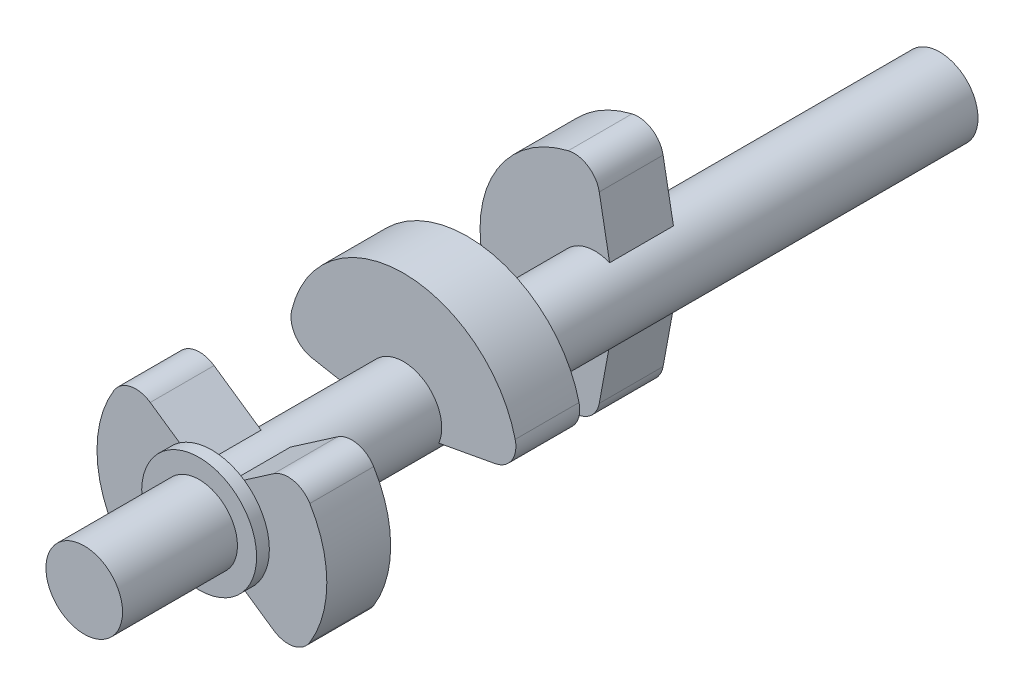
SolidWorks part; units mm, degrees
ref_plane "Спереди" through (0, 0, 0) normal (0, 0, 1) x (1, 0, 0)
ref_plane "Сверху" through (0, 0, 0) normal (0, 1, 0) x (1, 0, 0)
ref_plane "Справа" through (0, 0, 0) normal (1, 0, 0) x (0, 0, -1)
sketch "Эскиз2" plane through (0, 0, 0) normal (0, 0, 1) x (1, 0, 0)
  circle A0 centre (0, 0) radius 1.5
  dimension "D1" = 3
extrude "shaft" add sketch "Эскиз2" along normal blind 33.5
ref_plane "excentric1plane" through (0, 0, 11) normal (0, 0, -1) x (-1, 0, 0)
sketch "Эскиз3" plane through (0, 0, 11) normal (0, 0, -1) x (-1, 0, 0)
  line L0 (1.7221, 4.1575) -> (0, 0) construction
  line L1 (0, 4.5) -> (0, 0) construction
  line L2 (3.182, 3.182) -> (0, 0) construction
  line L3 (4.1575, 1.7221) -> (0, 0) construction
  line L4 (4.5, 0) -> (0, 0) construction
  line L5 (4.1575, -1.7221) -> (0, 0) construction
  line L6 (3.182, -3.182) -> (0, 0) construction
  line L7 (1.7221, -4.1575) -> (0, 0) construction
  line L8 (0, -4.5) -> (0, 0) construction
  line L9 (-1.2555, -3.031) -> (-0.574, -1.3858) construction
  line L10 (-3.182, -3.182) -> (0, 0) construction
  line L11 (-4.1575, -1.7221) -> (0, 0) construction
  line L12 (-4.5, 0) -> (0, 0) construction
  line L13 (-4.1575, 1.7221) -> (0, 0) construction
  line L14 (-3.182, 3.182) -> (0, 0) construction
  line L15 (-1.2555, 3.031) -> (-0.574, 1.3858) construction
  line L16 (0, 4.5) -> (-0.574, 1.3858)
  line L17 (0, -4.5) -> (-0.574, -1.3858)
  circle A0 centre (0, 0) radius 4.5
  circle A1 centre (0, 0) radius 1.5
  point P21 (0, 0)
  dimension "D2" = 9
  dimension "D1" = 16
ref_plane "excentric2plane" through (0, 0, 18.5) normal (0, 0, -1) x (-1, 0, 0)
ref_plane "excentric3plane" through (0, 0, 26) normal (0, 0, -1) x (-1, 0, 0)
sketch "excentric2sketch" plane through (0, 0, 18.5) normal (0, 0, -1) x (-1, 0, 0)
  line L0 (1.7221, 4.1575) -> (0, 0) construction
  line L1 (0, 4.5) -> (0, 0) construction
  line L2 (3.182, 3.182) -> (0, 0) construction
  line L3 (4.1575, 1.7221) -> (0, 0) construction
  line L4 (4.5, 0) -> (0, 0) construction
  line L5 (3.031, -1.2555) -> (1.3858, -0.574) construction
  line L6 (3.182, -3.182) -> (0, 0) construction
  line L7 (1.7221, -4.1575) -> (0, 0) construction
  line L8 (0, -4.5) -> (0, 0) construction
  line L9 (-1.2555, -3.031) -> (-0.574, -1.3858) construction
  line L10 (-3.182, -3.182) -> (0, 0) construction
  line L11 (-3.031, -1.2555) -> (-1.3858, -0.574) construction
  line L12 (-4.5, 0) -> (0, 0) construction
  line L13 (-4.1575, 1.7221) -> (0, 0) construction
  line L14 (-3.182, 3.182) -> (0, 0) construction
  line L15 (-1.2555, 3.031) -> (-0.574, 1.3858) construction
  line L16 (-4.5, 0) -> (-1.3858, -0.574)
  line L17 (4.5, 0) -> (1.3858, -0.574)
  circle A0 centre (0, 0) radius 4.5
  circle A1 centre (0, 0) radius 1.5
  point P21 (0, 0)
  dimension "D2" = 9
  dimension "D1" = 16
sketch "excentric3sketch" plane through (0, 0, 26) normal (0, 0, -1) x (-1, 0, 0)
  line L0 (1.7221, 4.1575) -> (0, 0) construction
  line L1 (0, 4.5) -> (0, 0) construction
  line L2 (3.182, 3.182) -> (0, 0) construction
  line L3 (4.1575, 1.7221) -> (0, 0) construction
  line L4 (4.5, 0) -> (0, 0) construction
  line L5 (4.1575, -1.7221) -> (0, 0) construction
  line L6 (3.182, -3.182) -> (0, 0) construction
  line L7 (1.7221, -4.1575) -> (0, 0) construction
  line L8 (0, -4.5) -> (0, 0) construction
  line L9 (-1.2555, -3.031) -> (-0.574, -1.3858) construction
  line L10 (-3.182, -3.182) -> (0, 0) construction
  line L11 (-4.1575, -1.7221) -> (0, 0) construction
  line L12 (-4.5, 0) -> (0, 0) construction
  line L13 (-4.1575, 1.7221) -> (0, 0) construction
  line L14 (-3.182, 3.182) -> (0, 0) construction
  line L15 (-1.2555, 3.031) -> (-0.574, 1.3858) construction
  line L16 (3.182, 3.182) -> (0.574, 1.3858)
  line L17 (3.182, -3.182) -> (0.574, -1.3858)
  line L18 (-3.182, -3.182) -> (-0.574, -1.3858)
  line L19 (-3.182, 3.182) -> (-0.574, 1.3858)
  circle A0 centre (0, 0) radius 4.5
  circle A1 centre (0, 0) radius 1.5
  point P21 (0, 0)
  dimension "D2" = 9
  dimension "D1" = 16
extrude "excentric1" add sketch "Эскиз3" against normal blind 2.5 contours A1 L17 A0 L16
extrude "Бобышка-Вытянуть3" add sketch "excentric2sketch" against normal blind 2.5 contours A1 L17 A0 L16
extrude "Бобышка-Вытянуть4" add sketch "excentric3sketch" against normal blind 2.5 contours A1 L19 A0 L18 | A1 L17 A0 L16
fillet "Скругление1" radius 1 8 edges at (-3.182, 3.182, 27.25) (3.182, 3.182, 27.25) (3.182, -3.182, 27.25) (-3.182, -3.182, 27.25) (-4.5, 0, 19.75) (4.5, 0, 19.75) (0, -4.5, 12.25) (0, 4.5, 12.25)
sketch "Эскиз7" plane through (0, 0, 28.5) normal (0, 0, 1) x (1, 0, 0)
  circle A0 centre (0, 0) radius 2.25
  dimension "D1" = 4.5
extrude "Бобышка-Вытянуть5" add sketch "Эскиз7" along normal blind 0.5
